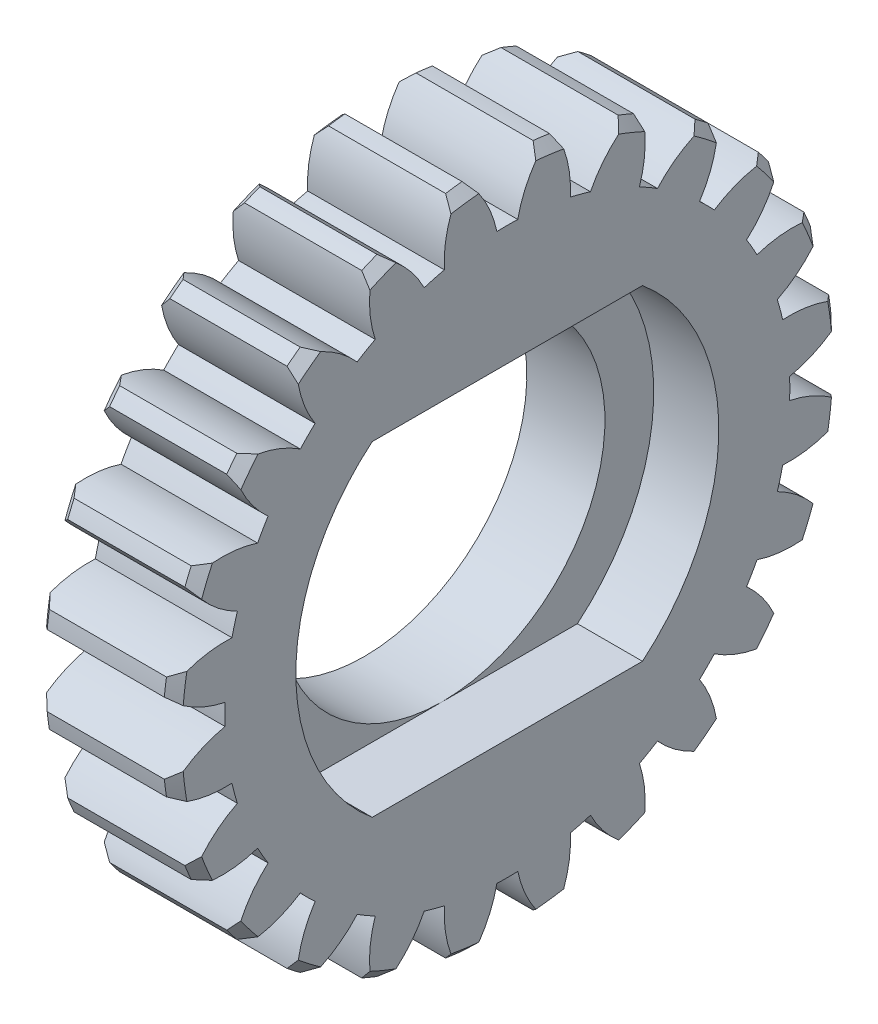
SolidWorks part; units mm, degrees
ref_plane "Plane1" through (0, 0, 0) normal (0, 0, 1) x (1, 0, 0)
ref_plane "Plane2" through (0, 0, 0) normal (0, 1, 0) x (1, 0, 0)
ref_plane "Plane3" through (0, 0, 0) normal (1, 0, 0) x (0, 0, -1)
sketch "HoldingSke" plane through (0, 0, 0) normal (0, 1, 0) x (1, 0, 0)
  line L0 (0, 0) -> (1.2947, -0.6037)
  line L1 (-15, 0) -> (100, 0) construction
  line L2 (0, 0) -> (-2.1039, 2.3779)
  line L3 (0, 0) -> (-11.863, 4.5341)
  line L4 (0, 0) -> (7.8269, 3.6497)
  line L5 (0, 0) -> (-46.8476, -17.4728)
  line L6 (0, 0) -> (-4.1448, -2.7965)
  line L7 (-2.1039, 2.3779) -> (8.6586, 51.2059)
  line L8 (-76.2, 54.61) -> (-75.7, 54.61)
  line L9 (-71.009, 38.7566) -> (-53.1078, 45.2721)
  line L10 (-76.2, 71.12) -> (104.1128, 71.12)
  line L11 (0, 0) -> (-5, 0)
  line L12 (-76.2, 101.6) -> (-76.173, 101.6)
  line L13 (24.9733, 27.94) -> (52.9518, 28.4284)
  line L14 (24.9733, 27.94) -> (24.9743, 27.94)
  line L15 (24.9733, 27.94) -> (100.4006, 29.5858)
  line L16 (-63.627, -0.7) -> (-12.827, -0.7)
  circle A0 centre (0, 0) radius 1.5
  circle A1 centre (0, 0) radius 7.874
  circle A2 centre (0, 0) radius 37.5
  circle A3 centre (0, 0) radius 1.5
  dimension "MHD" = 15.748
  dimension "Hub_dia" = 75
  dimension "Bore" = 3
  dimension "MBD" = 3
  dimension "Num_teeth" = 25
  dimension "Pitch_radius" = 180.3128
  dimension "Pitch" = 1.4286
  dimension "Width" = 5
  dimension "Overall_len" = 50
  dimension "Show_teeth" = 25
  dimension "Thickness" = 5
  dimension "OAL" = 50.0001
  dimension "T_dim" = 0.5
  dimension "Ap" = 20
  dimension "H" = 19.05
  dimension "Backlash" = 0.027
  dimension "Addendum_fac" = 1
  dimension "Dedendum_fac" = 1.25
  dimension "Clearance_fac" = 0.25
  dimension "Dedendum_add" = 0.001
  dimension "Module" = 0.7
sketch "BasProSke" plane through (0, 0, 0) normal (0, 1, 0) x (1, 0, 0)
  line L0 (-10, 0) -> (60, 0) construction
  line L1 (0, 0) -> (0, 10.3)
  line L2 (0, 0) -> (4.2, 0)
  line L3 (4.2, 0) -> (4.2, 10.3)
  line L4 (4.2, 10.3) -> (0, 10.3)
  dimension "D2" = 4.2
  dimension "D1" = 10.3
revolve "Base-Revolve" add sketch "BasProSke" angle 360 about L0
chamfer "倒角1" distance 0.3 angle 45 2 edges at (4.2, 0, 10.3) (0, 0, 10.3)
sketch "TooCutSke" plane through (0, 0, 0) normal (1, 0, 0) x (0, 0, -1)
  line L1 (0, 0) -> (0, 107) construction
  line L2 (0, 0) -> (-0.7877, 9.8302) construction
  line L3 (0, 0) -> (-2.5711, 19.5293) construction
  line L4 (-0.7877, 9.8302) -> (-1.2855, 9.7646) construction
  arc A0 (0.321, 8.6758) -> (-0.321, 8.6758) centre (0, 0) ccw
  arc A1 (1.0918, 10.242) -> (-1.0918, 10.242) centre (0, 0) ccw
  circle A3 centre (0, 0) radius 8.8 construction
  arc A4 (-0.321, 8.6758) -> (-1.0918, 10.242) centre (-3.7475, 7.9622) ccw
  arc A5 (1.0918, 10.242) -> (0.321, 8.6758) centre (3.7475, 7.9622) ccw
  dimension "D2" = 17.6
  dimension "Overcut_dia" = 20.6
  dimension "Flank_rad" = 3.5
  dimension "Half_ang" = 7.5
  dimension "Half_CT" = 0.5022
extrude "ToothCut" cut sketch "TooCutSke" along normal through all
fillet "Breaks" [suppressed] radius 0.014
fillet "RootFillets" [suppressed] radius 0.176
pattern_circular "TeethCuts" count 24 every 15 about axis through (-10, 0, 0) along (1, 0, 0) of "ToothCut"
sketch "HubNeaOneSke" plane through (0, 0, 0) normal (-1, 0, 0) x (0, 0, 1)
  circle A0 centre (0, 0) radius 7.874
  dimension "Diameter" = 15.748
extrude "HubNearOne" [suppressed] add sketch "HubNeaOneSke" along normal blind 45.0001
sketch "HubNeaBotSke" plane through (0, 0, 0) normal (-1, 0, 0) x (0, 0, 1)
  circle A0 centre (0, 0) radius 7.874
  dimension "Diameter" = 15.748
extrude "HubNearBoth" [suppressed] add sketch "HubNeaBotSke" along normal blind 22.5
ref_plane "FarPln" through (5, 0, 0) normal (1, 0, 0) x (0, 0, -1)
sketch "HubFarSke" plane through (5, 0, 0) normal (1, 0, 0) x (0, 0, -1)
  circle A0 centre (0, 0) radius 7.874
  dimension "Diameter" = 15.748
extrude "HubFar" [suppressed] add sketch "HubFarSke" along normal blind 22.5
sketch "BorSke" plane through (0, 0, 0) normal (1, 0, 0) x (0, 0, -1)
  circle A0 centre (0, 0) radius 1.5
  dimension "Diameter" = 3
extrude "Bore" cut sketch "BorSke" along normal mid plane 100.0001
sketch "KeySke" plane through (0, 0, 0) normal (1, 0, 0) x (0, 0, -1)
  line L0 (-0.6, 0) -> (-0.6, 2)
  line L1 (-0.6, 2) -> (0.6, 2)
  line L2 (0.6, 2) -> (0.6, 0)
  line L3 (0, 0) -> (0, 34) construction
  line L4 (-0.6, 0) -> (0.6, 0)
  dimension "Offset" = 2
  dimension "Width" = 1.2
extrude "Keyway" [suppressed] cut sketch "KeySke" along normal mid plane 100.0001
pattern_circular "Keyway2" [suppressed] count 2 every 90 about axis through (-10, 0, 0) along (1, 0, 0)
sketch "草图1" plane through (4.2, 0, 0) normal (1, 0, 0) x (0, 0, -1)
  line L0 (-4.1533, 5) -> (4.1533, 5)
  line L1 (-6.5, 0) -> (6.5, 0) construction
  line L2 (-4.1533, -5) -> (4.1533, -5)
  arc A0 (4.1533, -5) -> (4.1533, 5) centre (0, 0) ccw
  arc A1 (-4.1533, 5) -> (-4.1533, -5) centre (0, 0) ccw
  dimension "D1" = 13
  dimension "D2" = 5
extrude "切除-拉伸1" cut sketch "草图1" against normal blind 2
sketch "草图2" plane through (2.2, 0, 0) normal (1, 0, 0) x (0, 0, -1)
  circle A0 centre (0, 0) radius 5
  dimension "D1" = 10
extrude "切除-拉伸2" cut sketch "草图2" against normal up to next
sketch "草图3" plane through (0, 0, 0) normal (-1, 0, 0) x (0, 0, 1)
  circle A0 centre (0, 0) radius 5 construction
  circle A1 centre (0, 0) radius 5
  circle A2 centre (0, 0) radius 6.1
  dimension "D1" = 12.2
extrude "凸台-拉伸1" add sketch "草图3" along normal blind 0.2
equation "' \"Module@HoldingSke\" = 6.35"
equation "' \"Num_teeth@HoldingSke\" = 12"
equation "' \"Ap@HoldingSke\" =  20"
equation "' \"Width@HoldingSke\" = 0.5 * 25.4"
equation "' \"Hub_dia@HoldingSke\"= 1 * 25.4"
equation "' \"Overall_len@HoldingSke\" = 1.0 * 25.4"
equation "' \"Bore@HoldingSke\" = 0.75 * 25.4"
equation "' \"T_dim@HoldingSke\" = 0.1 * 25.4"
equation "' \"Width@KeySke\" = 0.25 * 25.4"
equation "' \"Show_teeth@HoldingSke\" = 13"
equation "' \"Backlash@HoldingSke\" = 0.009 * 25.4"
equation "' \"Addendum_fac@HoldingSke\" = 1.0"
equation "' \"Dedendum_fac@HoldingSke\" = 1.25"
equation "' \"Dedendum_add@HoldingSke\" = 0.00005 * 25.4"
equation "' \"Clearance_fac@HoldingSke\" = 0.25"
